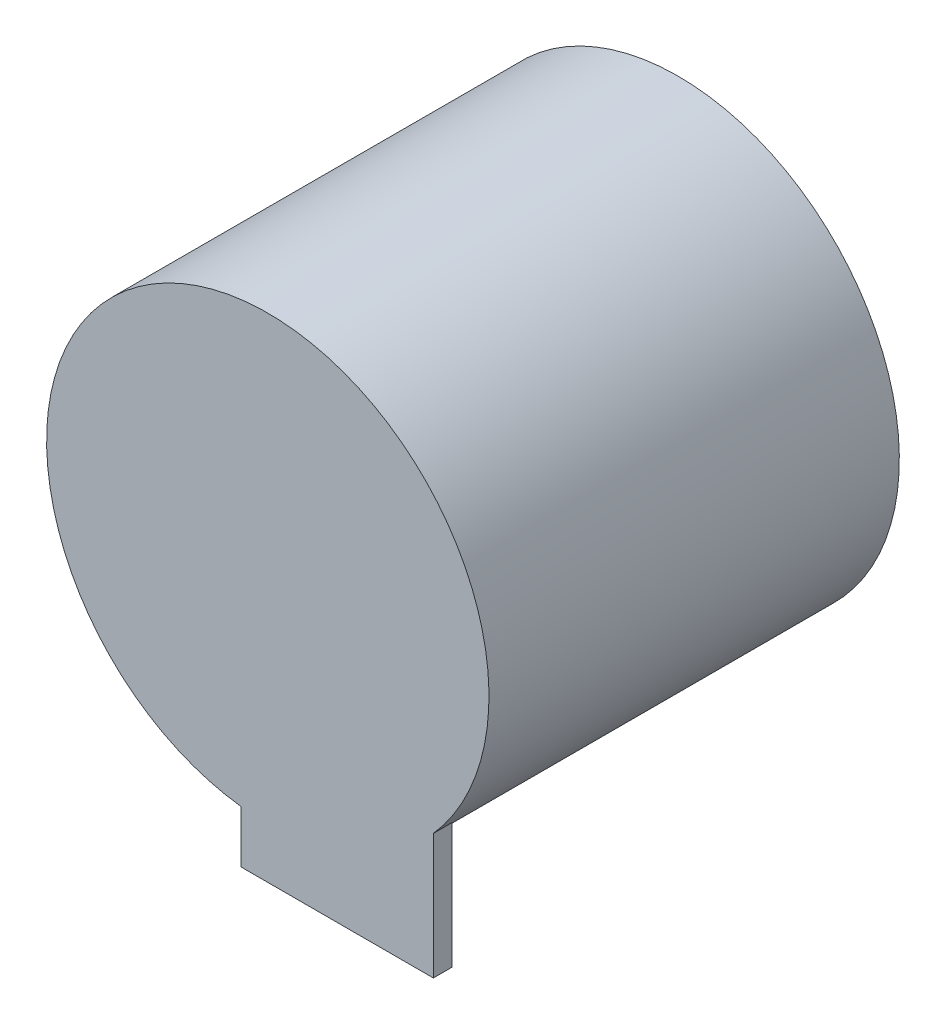
SolidWorks part; units mm, degrees
ref_plane "Front Plane" through (0, 0, 0) normal (0, 0, 1) x (1, 0, 0)
ref_plane "Top Plane" through (0, 0, 0) normal (0, 1, 0) x (1, 0, 0)
ref_plane "Right Plane" through (0, 0, 0) normal (1, 0, 0) x (0, 0, -1)
sketch "Sketch1" plane through (-36.2725, 0, 0) normal (0, 0, -1) x (-1, 0, 0)
  circle A0 centre (-36.2725, 0) radius 23.5
  dimension "D1" = 47
extrude "Boss-Extrude1" add sketch "Sketch1" along normal mid plane 43.6
sketch "Sketch2" plane through (0, 0, 21.8) normal (0, 0, 1) x (1, 0, 0)
  line L1 (-2.8276, -13.5749) -> (17.5898, -13.5749)
  line L2 (-2.8276, -13.5749) -> (-2.8276, -28.888)
  line L3 (-2.8276, -28.888) -> (17.5898, -28.888)
  line L4 (17.5898, -13.5749) -> (17.5898, -28.888)
extrude "Boss-Extrude2" add sketch "Sketch2" against normal blind 2
